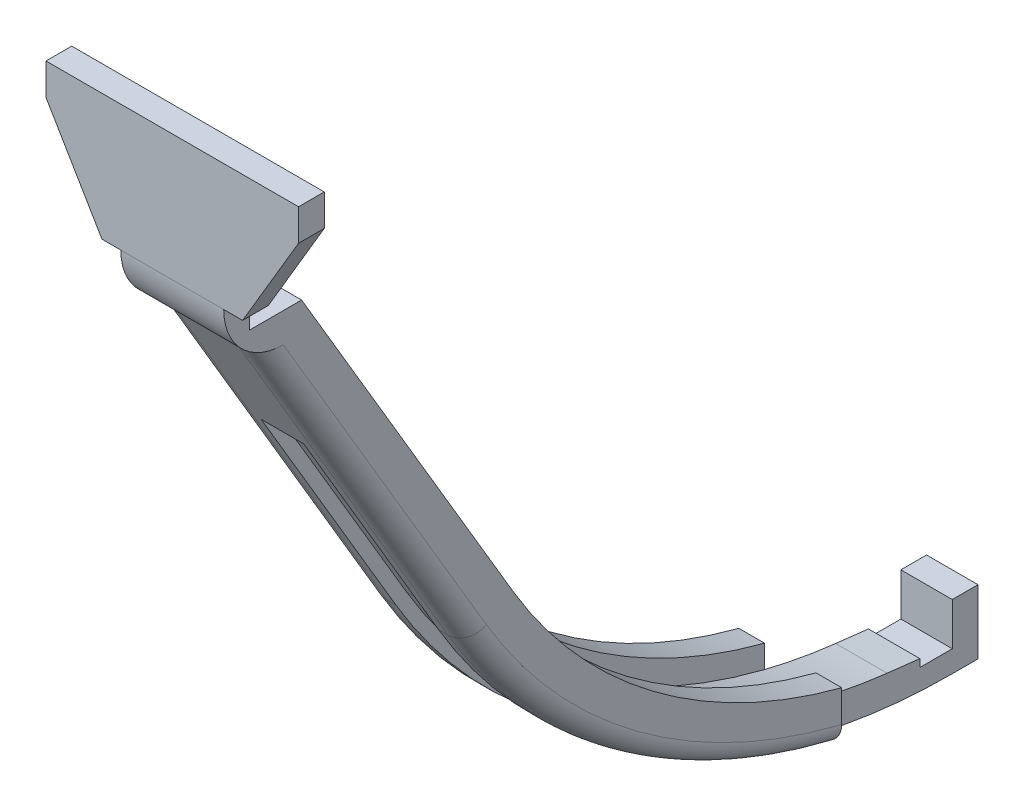
SolidWorks part; units mm, degrees
ref_plane "Front Plane" through (0, 0, 0) normal (0, 0, 1) x (1, 0, 0)
ref_plane "Top Plane" through (0, 0, 0) normal (0, 1, 0) x (1, 0, 0)
ref_plane "Right Plane" through (0, 0, 0) normal (1, 0, 0) x (0, 0, -1)
sketch "Sketch1" plane through (0, 0, 0) normal (0, 1, 0) x (1, 0, 0)
  circle A0 centre (0, 0) radius 30
  dimension "D1" = 60
sketch "Sketch3" plane through (0, 0, 0) normal (1, 0, 0) x (0, 0, -1)
  line L0 (0, 16.1146) -> (0, -58.8622) construction
sketch "Sketch2" plane through (0, 0, 0) normal (1, 0, 0) x (0, 0, -1)
  line L1 (30, 0) -> (-30, 0) construction
  line L2 (0, -50.8) -> (-30, 0)
  line L4 (0, 0) -> (0, -50.8)
  line L5 (-30, 0) -> (0, 0)
  dimension "D1" = 30
revolve "Revolve1" add sketch "Sketch2" angle 360 about L4
sketch "Sketch4" plane through (0, 0, 0) normal (1, 0, 0) x (0, 0, -1)
  line L0 (0, -45.72) -> (-24.92, 0)
  line L1 (0, 16.1146) -> (0, -58.8622) construction
  line L2 (30, 0) -> (-30, 0) construction
  line L3 (-24.92, 0) -> (0, 0)
  line L4 (0, 0) -> (0, -45.72)
  dimension "D1" = 5.08
  dimension "D2" = 5.08
revolve "Cut-Revolve1" cut sketch "Sketch4" angle 360 about L0
sketch "Sketch5" plane through (0, 0, 0) normal (1, 0, 0) x (0, 0, -1)
  line L0 (0, 16.1146) -> (0, -58.8622) construction
  line L1 (6.44, -39.8949) -> (-6.44, -39.8949)
  line L2 (6.44, -39.8949) -> (6.44, -55.7296)
  line L3 (6.44, -55.7296) -> (-6.44, -55.7296)
  line L4 (-6.44, -39.8949) -> (-6.44, -55.7296)
  line L5 (0, -50.8) -> (30, 0) construction
  line L6 (-24.92, 0) -> (0, -45.72) construction
  line L7 (30, 0) -> (-30, 0) construction
  line L8 (0, -45.72) -> (24.92, 0) construction
  point P4 (0, -39.8949)
  point P7 (3.175, -39.8949)
  point P18 (-3.175, -39.8949)
  dimension "D1" = 6.35
  dimension "D2" = 5.08
  dimension "D3" = 5.08
extrude "Cut-Extrude2" cut sketch "Sketch5" against normal mid plane 15.24
ref_plane "Plane1" through (0, 0, 30) normal (0, 0, 1) x (1, 0, 0)
sketch "Sketch11" plane through (0, 0, 30) normal (0, 0, 1) x (1, 0, 0)
  line L0 (30, 0) -> (-30, 0) construction
  line L1 (6.35, 0) -> (3.175, 0)
  line L2 (6.35, 0) -> (6.35, -3.175)
  line L3 (6.35, -3.175) -> (3.175, -3.175)
  line L4 (3.175, 0) -> (3.175, -3.175)
  line L5 (3.175, -3.175) -> (-3.175, -3.175) construction
  line L6 (-3.175, 0) -> (-6.35, 0)
  line L7 (-3.175, 0) -> (-3.175, -3.175)
  line L8 (-3.175, -3.175) -> (-6.35, -3.175)
  line L9 (-6.35, 0) -> (-6.35, -3.175)
  point P10 (0, -3.175)
  dimension "D1" = 3.175
  dimension "D2" = 3.175
  dimension "D3" = 6.35
extrude "Cut-Extrude6" cut sketch "Sketch11" against normal up to next
sketch "Sketch6" plane through (0, 0, 0) normal (1, 0, 0) x (0, 0, -1)
  line L0 (-7.3746, -39.8949) -> (20.6187, -87.297)
  line L1 (83.5, -116.84) -> (83.5, -115.2525)
  line L2 (83.5, -115.2525) -> (86.675, -115.2525)
  line L3 (86.675, -115.2525) -> (86.675, -123.19)
  line L5 (0, -39.8949) -> (26.0865, -84.068)
  line L6 (-30, 0) -> (-6.44, -39.8949) construction
  line L7 (30, 0) -> (-30, 0) construction
  line L8 (0, 16.1146) -> (0, -58.8622) construction
  line L11 (0, -39.8949) -> (-23.56, 0)
  line L12 (0, -39.8949) -> (-7.3746, -39.8949)
  line L13 (-23.56, 0) -> (-30.9346, 0)
  line L14 (-7.3746, -39.8949) -> (-30.9346, 0)
  line L15 (-6.44, -39.8949) -> (6.44, -39.8949) construction
  line L16 (83.5, -123.19) -> (86.675, -123.19)
  arc A0 (20.6187, -87.297) -> (63.5, -120.3979) centre (83.5, -50.1624) ccw
  arc A1 (26.0865, -84.068) -> (83.5, -116.84) centre (83.5, -50.1624) ccw
  arc A2 (63.5, -120.3979) -> (83.5, -123.19) centre (83.5, -50.1624) ccw
  dimension "D1" = 3.175
  dimension "D3" = 1.5875
  dimension "D2" = 6.35
  dimension "D4" = 6.35
  dimension "D5" = 123.19
  dimension "D6" = 63.5
  dimension "D7" = 20
extrude "Boss-Extrude1" add sketch "Sketch6" along normal mid plane 12.7
sketch "Sketch7" plane through (0, 0, 0) normal (1, 0, 0) x (0, 0, -1)
  line L0 (-3.175, -39.8949) -> (23.7324, -85.4582)
  line L1 (26.0865, -84.068) -> (0, -39.8949) construction
  line L2 (0, 16.1146) -> (0, -58.8622) construction
  line L3 (-3.175, -39.8949) -> (-26.735, 0)
  line L4 (30, 0) -> (-30, 0) construction
  line L5 (-1.0729, -39.8949) -> (0, -39.8949) construction
  line L8 (-23.56, 0) -> (-26.735, 0)
  line L9 (26.0865, -84.068) -> (-23.56, 0)
  line L10 (83.5, -120.015) -> (83.5, -116.84)
  arc A0 (23.7324, -85.4582) -> (75.4573, -119.1063) centre (83.5, -50.1624) ccw
  arc A1 (26.0865, -84.068) -> (83.5, -116.84) centre (83.5, -50.1624) ccw construction
  arc A7 (75.4573, -119.1063) -> (83.5, -120.015) centre (204.6904, 988.7119) ccw
  arc A8 (26.0865, -84.068) -> (83.5, -116.84) centre (83.5, -50.1624) ccw construction
  arc A9 (83.5, -116.84) -> (26.0865, -84.068) centre (83.5, -50.1624) cw
  dimension "D1" = 3.175
  dimension "D2" = 3.175
extrude "Cut-Extrude4" cut sketch "Sketch7" against normal blind 3.175 contours L0 A0 A7 L10 A9 L9 L8 L3
mirror "Mirror1" about plane through (0, 0, 0) normal (1, 0, 0) of "Cut-Extrude4"
sketch "Sketch9" plane through (0, 0, 0) normal (1, 0, 0) x (0, 0, -1)
  line L0 (0, 0) -> (-24.92, 0)
  line L1 (-24.92, 0) -> (-0.5365, -39.8949)
  line L2 (-1.0729, -39.8949) -> (0, -39.8949) construction
  line L3 (-0.5365, -39.8949) -> (0, -39.8949)
  line L4 (0, -39.8949) -> (0, 0)
  dimension "D1" = 24.92
revolve "Cut-Revolve2" cut sketch "Sketch9" angle 360 about L0
sketch "Sketch10" plane through (-6.35, 0, 0) normal (-1, 0, 0) x (0, 0, 1)
  line L0 (-83.5, -116.84) -> (-83.5, -115.2525) construction
  line L1 (-83.5, -116.7199) -> (-79.5, -116.7199)
  line L2 (-83.5, -116.7199) -> (-83.5, -120.015)
  line L3 (-83.5, -120.015) -> (-79.5, -120.015)
  line L4 (-79.5, -116.7199) -> (-79.5, -120.015)
  line L6 (-83.5, -120.015) -> (-79.5, -120.015)
  line L7 (-83.5, -120.015) -> (-83.5, -120.515)
  line L8 (-83.5, -120.515) -> (-79.5, -120.515)
  line L9 (-79.5, -120.015) -> (-79.5, -120.515)
  arc A0 (-83.5, -116.84) -> (-26.0865, -84.068) centre (-83.5, -50.1624) ccw construction
  arc M9 (-26.0865, -84.068) -> (-83.5, -116.84) centre (-83.5, -50.1624) cw
  dimension "D1" = 0.5
  dimension "D2" = 4
extrude "Cut-Extrude5" cut sketch "Sketch10" against normal through all contours L4 L2 L3 M9 | L9 L3 L7 L8
sketch "Sketch12" plane through (0, 0, 0) normal (-1, 0, 0) x (0, 0, 1)
  line L1 (30, 0) -> (-30, 0)
  line L2 (-30, 0) -> (-30, -39.8949)
  line L6 (30, 0) -> (-30, 0) construction
  line L7 (29.3203, 0) -> (30.9346, 0) construction
  line L9 (-6.44, -39.8949) -> (-30, -39.8949)
  line L11 (6.44, -39.8949) -> (30, 0)
  line L12 (-6.44, -39.8949) -> (6.44, -39.8949)
  line L13 (0, 16.1146) -> (0, -58.8622) construction
  dimension "D1" = 30
  dimension "D2" = 6.44
extrude "Cut-Extrude7" cut sketch "Sketch12" against normal mid plane 81.28
sketch "Sketch13" plane through (0, -13.5447, 22.9358) normal (0, -0.5085, 0.8611) x (1, 0, 0)
  line L1 (-6.35, 15.7303) -> (-28.6819, 15.7303)
  line L2 (-6.35, 15.7303) -> (-6.35, -41.1116)
  line L3 (-6.35, -41.1116) -> (-28.6819, -41.1116)
  line L4 (-28.6819, 15.7303) -> (-28.6819, -41.1116)
  line L5 (6.35, 15.7303) -> (27.8907, 15.7303)
  line L6 (6.35, 15.7303) -> (6.35, -42.7196)
  line L7 (6.35, -42.7196) -> (27.8907, -42.7196)
  line L8 (27.8907, 15.7303) -> (27.8907, -42.7196)
extrude "Cut-Extrude8" [suppressed] cut sketch "Sketch13" against normal through all
sketch "Sketch18" plane through (-6.35, 0, 0) normal (-1, 0, 0) x (0, 0, 1)
  line L0 (6.44, -39.8949) -> (6.44, -20.5)
  line L2 (6.44, -20.5) -> (9.615, -20.5)
  line L3 (9.615, -20.5) -> (9.615, -34.5186)
  line L6 (9.615, -34.5186) -> (9.615, -36.1012)
  line L7 (-20.6187, -87.297) -> (30.9346, 0) construction
  line L8 (5.7568, -42.6345) -> (6.44, -41.4775)
  line L9 (6.44, -41.4775) -> (6.44, -39.8949)
  line L10 (30, 0) -> (-30, 0) construction
  line L11 (30, 0) -> (6.44, -39.8949) construction
  arc A1 (9.615, -36.1012) -> (5.7568, -42.6345) centre (2.1544, -36.1012) cw
  point P14 (8.5784, -39.8949)
  dimension "D1" = 3.175
  dimension "D2" = 20.5
extrude "Boss-Extrude3" add sketch "Sketch18" against normal up to surface (12.7 mm away) up to face at (6.35, -84.6761, -42.5653)
sketch "Sketch19" plane through (-6.35, 0, 0) normal (-1, 0, 0) x (0, 0, 1)
  line L0 (9.615, 0) -> (9.615, -36.1012)
  line L1 (9.615, -36.1012) -> (30.9346, -36.1012)
  line L2 (30.9346, -36.1012) -> (30.9346, 0)
  line L3 (30.9346, 0) -> (9.615, 0)
  line L4 (-20.6187, -87.297) -> (5.7568, -42.6345) construction
  line L5 (9.615, -34.5186) -> (9.615, -20.5) construction
extrude "Cut-Extrude10" cut sketch "Sketch19" against normal through all
sketch "Sketch21" plane through (0, 0, 9.615) normal (0, 0, 1) x (1, 0, 0)
  line L1 (-6.35, -20.5) -> (-15.5875, -20.5)
  line L2 (-6.35, -20.5) -> (-6.35, -23.675)
  line L3 (-6.35, -23.675) -> (-15.5875, -23.675)
  line L4 (-15.5875, -20.5) -> (-15.5875, -23.675)
  line L5 (6.35, -20.5) -> (15.5875, -20.5)
  line L6 (6.35, -20.5) -> (6.35, -23.675)
  line L7 (6.35, -23.675) -> (15.5875, -23.675)
  line L8 (15.5875, -20.5) -> (15.5875, -23.675)
  line L9 (-15.5875, -23.675) -> (-6.35, -23.675)
  line L10 (-15.5875, -23.675) -> (-15.5875, -36.1012)
  line L11 (-15.5875, -36.1012) -> (-6.35, -36.1012)
  line L12 (-6.35, -23.675) -> (-6.35, -36.1012)
  line L13 (15.5875, -23.675) -> (6.35, -23.675)
  line L14 (15.5875, -23.675) -> (15.5875, -36.1012)
  line L15 (15.5875, -36.1012) -> (6.35, -36.1012)
  line L16 (6.35, -23.675) -> (6.35, -36.1012)
  line M9 (-6.35, -20.5) -> (-6.35, -36.1012)
  line M11 (6.35, -36.1012) -> (6.35, -20.5)
  dimension "D1" = 31.175
  dimension "D2" = 3.175
extrude "Boss-Extrude4" add sketch "Sketch21" against normal up to surface (3.175 mm away) contours L10 L11 L3 M9 | L15 L14 L7 M11 | L8 L5 L7 M11 | L1 L4 L3 M9 up to face at (0, -30.1975, 6.44)
sketch "Sketch17" plane through (0, 0, -86.675) normal (0, 0, -1) x (-1, 0, 0)
  line L0 (-6.35, -84.068) -> (-6.35, -116.7199) construction
  line L1 (-6.35, -70.6178) -> (-3.175, -70.6178)
  line L2 (-6.35, -70.6178) -> (-6.35, -123.19)
  line L3 (-6.35, -123.19) -> (-3.175, -123.19)
  line L4 (-3.175, -70.6178) -> (-3.175, -123.19)
  line L5 (-6.35, -123.19) -> (6.35, -123.19) construction
  line L6 (3.175, -84.068) -> (3.175, -116.7199) construction
  line L7 (3.175, -70.6178) -> (6.35, -70.6178)
  line L8 (3.175, -70.6178) -> (3.175, -123.19)
  line L9 (3.175, -123.19) -> (6.35, -123.19)
  line L10 (6.35, -70.6178) -> (6.35, -123.19)
  line L11 (-3.175, -116.7199) -> (-3.175, -84.068) construction
extrude "Cut-Extrude9" cut sketch "Sketch17" against normal blind 20
sketch "Sketch22" plane through (0, 0, 6.44) normal (0, 0, -1) x (-1, 0, 0)
  line L0 (-15.5875, -24.4052) -> (-15.5875, -36.1012)
  line L1 (-15.5875, -20.5) -> (-15.5875, -36.1012) construction
  line L2 (-15.5875, -36.1012) -> (-8.6804, -36.1012)
  line L3 (-15.5875, -36.1012) -> (-6.35, -36.1012) construction
  line L4 (-8.6804, -36.1012) -> (-15.5875, -24.4052)
  line L5 (15.5875, -24.4052) -> (8.6804, -36.1012)
  line L6 (15.5875, -20.5) -> (15.5875, -36.1012) construction
  line L8 (8.6804, -36.1012) -> (15.5875, -36.1012)
  line L9 (15.5875, -36.1012) -> (15.5875, -24.4052)
  dimension "D1" = 6.9071
  dimension "D2" = 11.696
extrude "Cut-Extrude11" cut sketch "Sketch22" against normal through all
sketch "Sketch24" plane through (0, 0, 0) normal (1, 0, 0) x (0, 0, -1)
  line L0 (3.9859, -59.1321) -> (20.6187, -87.297)
  line L2 (20.6187, -87.297) -> (-5.7568, -42.6345) construction
  line L3 (66.675, -121.2254) -> (66.675, -119.683)
  line L4 (66.675, -117.5039) -> (66.675, -121.2254) construction
  line L5 (3.9859, -59.1321) -> (5.2775, -58.3694)
  line L6 (5.2775, -58.3694) -> (21.9103, -86.5342)
  arc A0 (20.6187, -87.297) -> (66.675, -121.2254) centre (83.5, -50.1624) ccw
  arc A1 (21.9103, -86.5342) -> (66.675, -119.683) centre (83.5, -50.1624) ccw
  dimension "D1" = 1.5
extrude "Cut-Extrude12" cut sketch "Sketch24" against normal mid plane 5.25
fillet "Fillet1" radius 2.54 4 edges at (6.35, -64.9657, -7.431) (-6.35, -64.9657, -7.431) (6.35, -108.9584, -40.1865) (-6.35, -108.9584, -40.1865)
